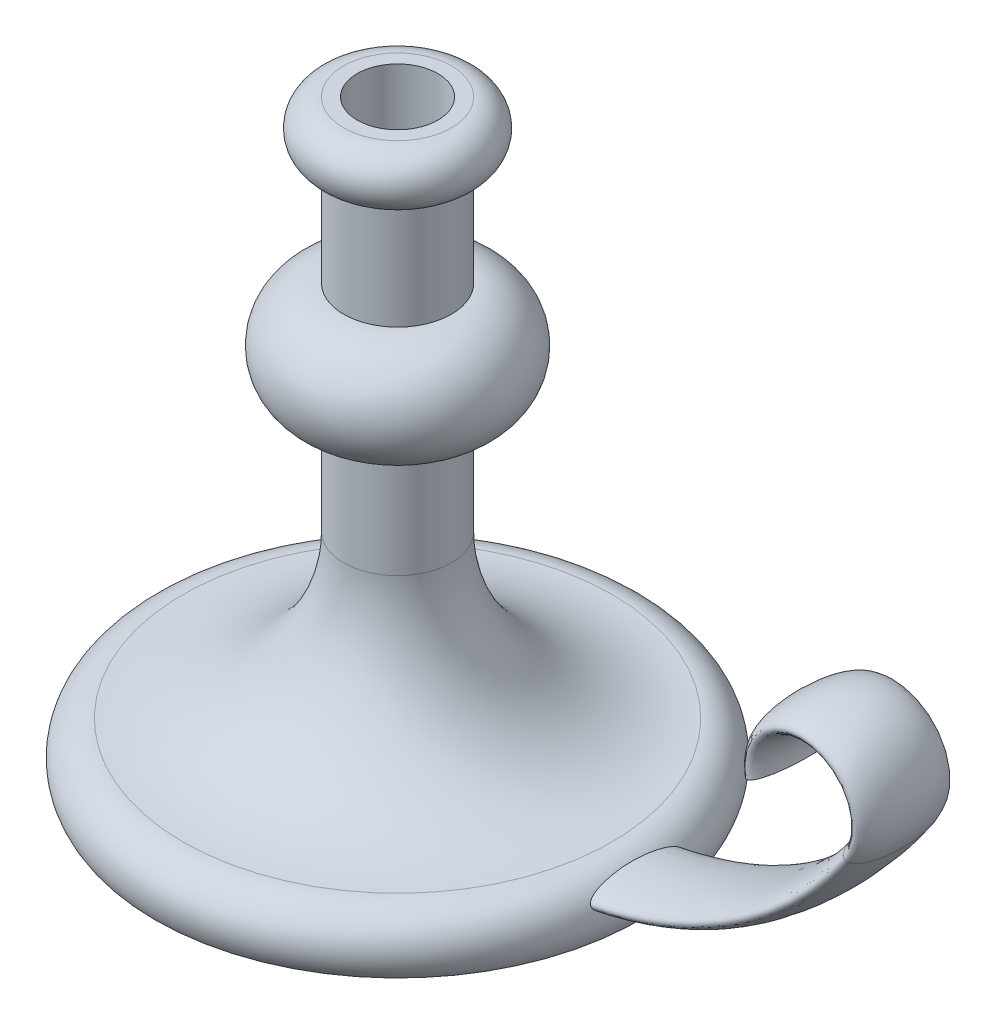
SolidWorks part; units mm, degrees
ref_plane "Front Plane" through (0, 0, 0) normal (0, 0, 1) x (1, 0, 0)
ref_plane "Top Plane" through (0, 0, 0) normal (0, 1, 0) x (1, 0, 0)
ref_plane "Right Plane" through (0, 0, 0) normal (1, 0, 0) x (0, 0, -1)
sketch "Sketch5" plane through (0, 0, 0) normal (0, 0, 1) x (1, 0, 0)
  line L0 (0, 0) -> (0, 220)
  line L1 (0, 220) -> (20, 220)
  line L2 (20, 200) -> (20, 160)
  line L3 (20, 120) -> (20, 80)
  line L4 (0, 0) -> (90, 0)
  arc A0 (20, 220) -> (20, 200) centre (20, 210) cw
  arc A1 (20, 160) -> (20, 120) centre (20, 140) cw
  arc A2 (20, 80) -> (79.7011, 20.0007) centre (80, 80) ccw
  arc A3 (79.7011, 20.0007) -> (90, 0) centre (79.6379, 7.3163) cw
  dimension "D3" = 10
  dimension "D5" = 20
  dimension "D7" = 60
  dimension "D1" = 220
  dimension "D2" = 20
  dimension "D4" = 40
  dimension "D6" = 40
  dimension "D8" = 90
revolve "Revolve1" add sketch "Sketch5" angle 360 about L0
sketch "Sketch6" plane through (0, 0, 0) normal (0, 0, 1) x (1, 0, 0)
  line L0 (0, 10) -> (60, 10)
  line L1 (0, 227.4356) -> (0, 175.1288) construction
  line L2 (-90, 0) -> (90, 0) construction
  arc A0 (60, 10) -> (183.5921, 75) centre (60, 160) ccw
  arc A1 (183.5921, 75) -> (147.4487, 82.685) centre (167.1131, 86.3333) ccw
  point P10 (0, 0)
  point P11 (0, 0)
  point P12 (0, 0)
  dimension "D2" = 150
  dimension "D3" = 20
  dimension "D1" = 60
  dimension "D4" = 65
  dimension "D5" = 10
sketch "Sketch7" plane through (0, 0, 0) normal (1, 0, 0) x (0, 0, -1)
  line L2 (0, 126.6554) -> (0, -13.3107) construction
  ellipse E0 centre (0, 10) end of major axis (-17.5, 10) minor radius 5
  dimension "D2" = 10
  dimension "D3" = 35
sweep "Sweep2" add profiles "Sketch7" path "Sketch6"
sketch "Sketch8" plane through (0, 220, 0) normal (0, 1, 0) x (1, 0, 0)
  circle A0 centre (0, 0) radius 15
  dimension "D1" = 30
extrude "Cut-Extrude1" cut sketch "Sketch8" against normal blind 25
